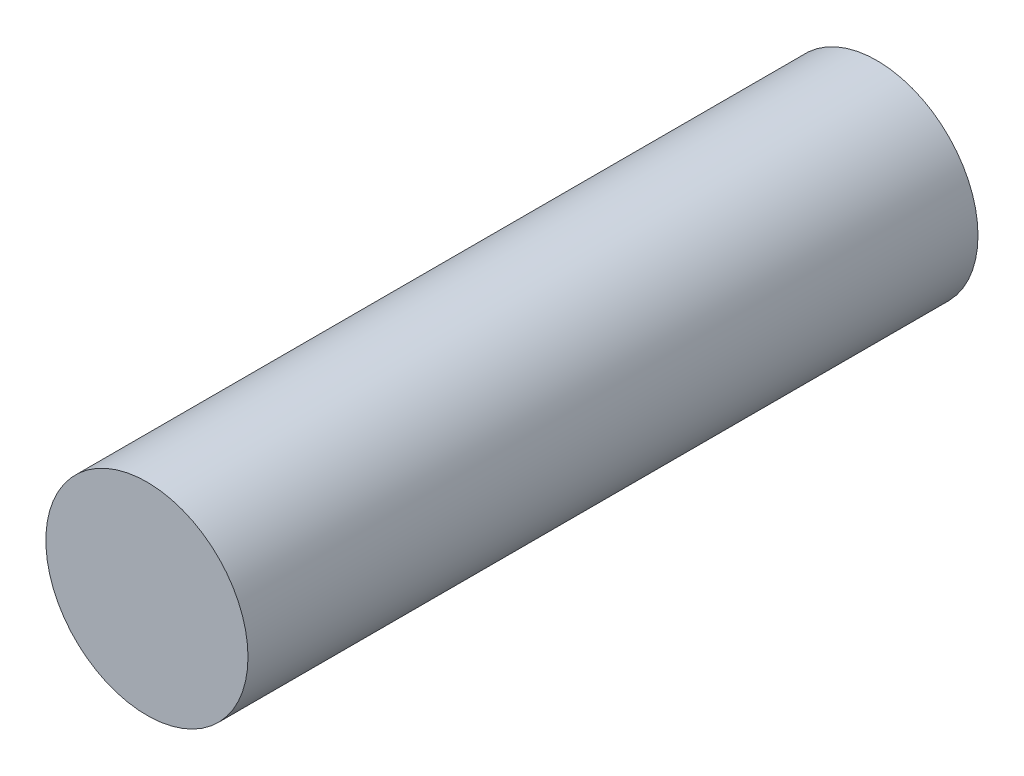
SolidWorks part; units mm, degrees
ref_plane "Спереди" through (0, 0, 0) normal (0, 0, 1) x (1, 0, 0)
ref_plane "Сверху" through (0, 0, 0) normal (0, 1, 0) x (1, 0, 0)
ref_plane "Справа" through (0, 0, 0) normal (1, 0, 0) x (0, 0, -1)
sketch "Эскиз1" plane through (0, 0, 0) normal (0, 0, 1) x (1, 0, 0)
  circle A0 centre (0, 0) radius 9
  dimension "D1" = 18
extrude "Бобышка-Вытянуть1" add sketch "Эскиз1" along normal blind 65
